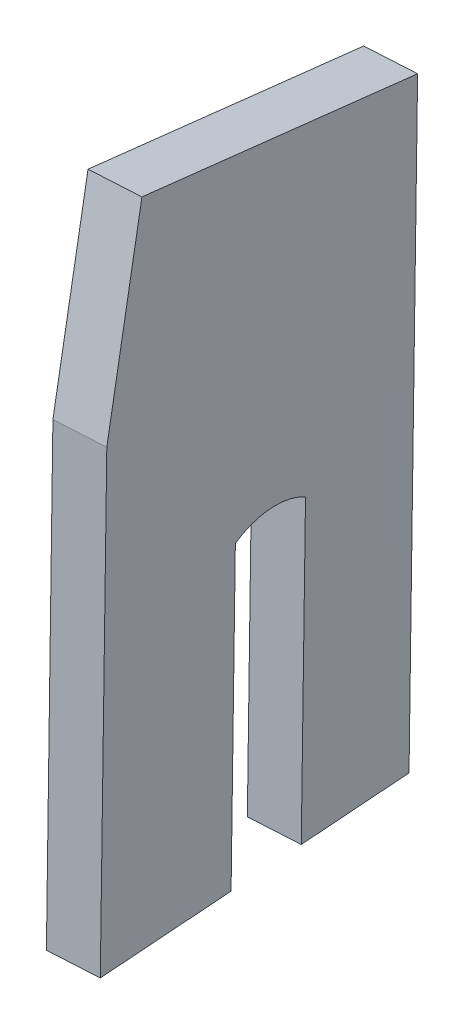
SolidWorks part; units mm, degrees
ref_plane "Front Plane" through (0, 0, 0) normal (0, 0, 1) x (1, 0, 0)
ref_plane "Top Plane" through (0, 0, 0) normal (0, 1, 0) x (1, 0, 0)
ref_plane "Right Plane" through (0, 0, 0) normal (1, 0, 0) x (0, 0, -1)
sketch "Sketch1" plane through (120.3404, -1.5, -8.5069) normal (0.9974, -0.0124, -0.0705) x (-0.0705, -0.0009, -0.9975)
  line L0 (-153.6761, -878.3071) -> (-145.5481, -878.3071) construction
  line L1 (-168.0634, -850.0039) -> (-92.5481, -418.4105) construction
  line L2 (-163.677, -824.9346) -> (-126.1558, -831.5506)
  line L7 (-149.2984, -853.2872) -> (-153.6761, -878.3071) construction
  line L8 (-136.5383, -855.5198) -> (-162.0586, -851.0546) construction
  line L11 (-150.3106, -870.0582) -> (-150.3106, -908.1582)
  line L12 (-150.3106, -908.1582) -> (-140.7856, -908.1582)
  line L13 (-140.7856, -870.0582) -> (-140.7856, -908.1582)
  line L14 (-168.0634, -908.1582) -> (-126.1558, -908.1582)
  line L15 (-126.1558, -831.5506) -> (-126.1558, -908.1582)
  line L16 (-163.677, -824.9346) -> (-168.0634, -850.0039)
  line L17 (-168.0634, -850.0039) -> (-168.0634, -908.1582)
  line L18 (-130.5335, -856.5705) -> (-55.0182, -424.9771) construction
  line L21 (-149.2984, -853.2872) -> (-117.6522, -858.8243) construction
  arc A1 (-140.7856, -870.0582) -> (-150.3106, -870.0582) centre (-145.5481, -878.3071) ccw
  line M3 (-86.5433, -419.4612) -> (-162.0586, -851.0546)
  line M4 (-162.0586, -851.0546) -> (-136.5383, -855.5198)
  line M5 (-136.5383, -855.5198) -> (-61.023, -423.9264)
  dimension "D8" = 9.525
  dimension "D1" = 8.128
  dimension "D2" = 90
  dimension "D3" = 9.525
  dimension "D5" = 38.1
  dimension "D4" = 9.525
  dimension "D6" = 25.4
  dimension "D7" = 90
  dimension "D9" = 25.4
  dimension "D10" = 100
extrude "Boss-Extrude1" add sketch "Sketch1" along normal blind 6.35 contours A1 L13 L14 L15 L2 L16 L17 L11 M5 M4 M3 | L2 M3 M4 M5
equation "\"Axle Diameter\"=0.75"
equation "\"D8@Sketch1\"=\"Axle Diameter\"/2"
